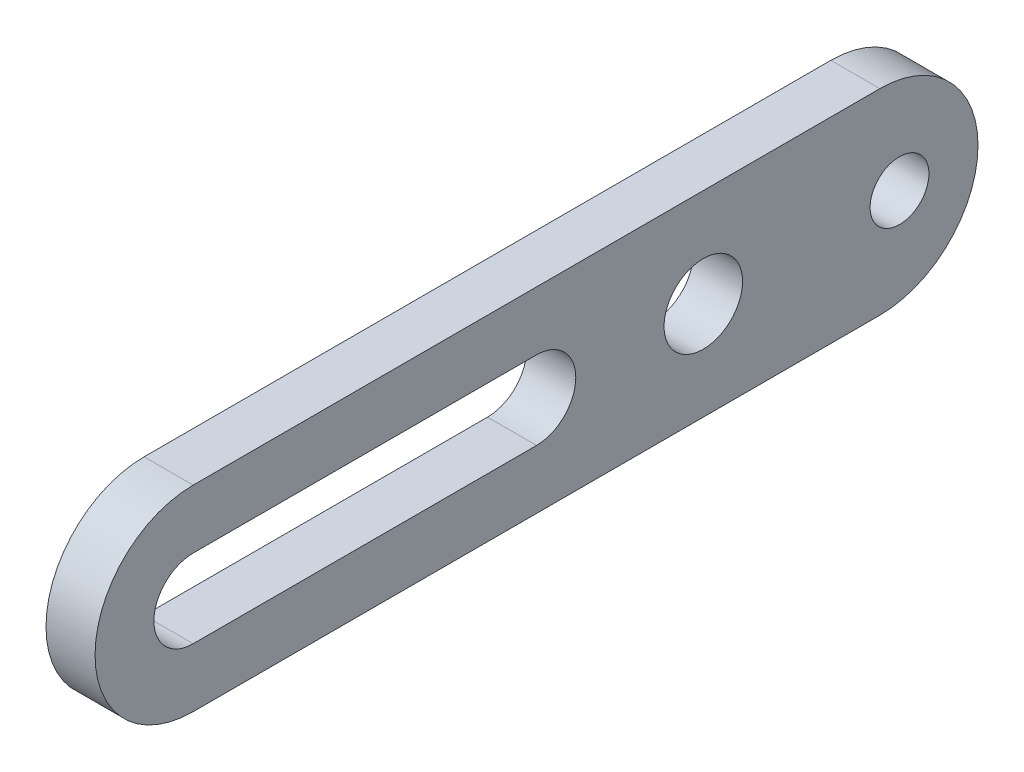
SolidWorks part; units mm, degrees
material "6061-T6 (SS)"
ref_plane "Front Plane" through (0, 0, 0) normal (0, 0, 1) x (1, 0, 0)
ref_plane "Top Plane" through (0, 0, 0) normal (0, 1, 0) x (1, 0, 0)
ref_plane "Right Plane" through (0, 0, 0) normal (1, 0, 0) x (0, 0, -1)
sketch "Sketch1" plane through (0, 0, 0) normal (1, 0, 0) x (0, 0, -1)
  line L0 (-35, 0) -> (35, 0) construction
  line L1 (-35, 10) -> (35, 10)
  line L2 (-35, -10) -> (35, -10)
  arc A0 (-35, 10) -> (-35, -10) centre (-35, 0) ccw
  arc A1 (35, -10) -> (35, 10) centre (35, 0) ccw
  point P3 (0, 0)
  dimension "D1" = 70
  dimension "D2" = 20
extrude "Boss-Extrude1" add sketch "Sketch1" along normal blind 5 contours L2 A1 L1 A0
sketch "Sketch2" plane through (5, 0, 0) normal (1, 0, 0) x (0, 0, -1)
  line L0 (-35, 0) -> (0, 0) construction
  line L1 (-35, 4) -> (0, 4)
  line L2 (-35, -4) -> (0, -4)
  circle A0 centre (17, 0) radius 4
  circle A1 centre (37, 0) radius 3
  arc A2 (-35, 4) -> (-35, -4) centre (-35, 0) ccw
  arc A3 (0, -4) -> (0, 4) centre (0, 0) ccw
  point P8 (-17.5, 0)
  dimension "D1" = 8
  dimension "D3" = 6
  dimension "D2" = 17
  dimension "D4" = 20
  dimension "D5" = 8
  dimension "D6" = 35
extrude "Cut-Extrude1" cut sketch "Sketch2" against normal through all
sketch "Sketch3" plane through (5, 0, 0) normal (1, 0, 0) x (0, 0, -1)
  line L1 (-49.2961, 16.0005) -> (50.7039, 16.0005)
  line L2 (-49.2961, 16.0005) -> (-49.2961, -13.9995)
  line L3 (-49.2961, -13.9995) -> (50.7039, -13.9995)
  line L4 (50.7039, 16.0005) -> (50.7039, -13.9995)
  dimension "D1" = 100
  dimension "D2" = 30
